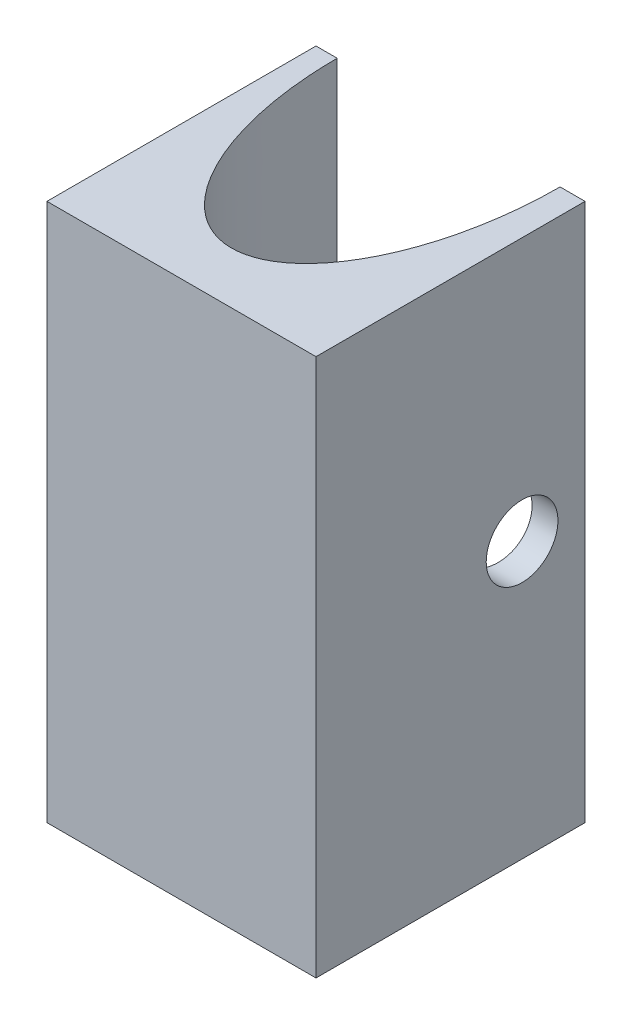
SolidWorks part; units mm, degrees
ref_plane "Front Plane" through (0, 0, 0) normal (0, 0, 1) x (1, 0, 0)
ref_plane "Top Plane" through (0, 0, 0) normal (0, 1, 0) x (1, 0, 0)
ref_plane "Right Plane" through (0, 0, 0) normal (1, 0, 0) x (0, 0, -1)
sketch "Sketch1" plane through (0, 0, 0) normal (0, 1, 0) x (1, 0, 0)
  line L1 (-48.6482, -19.1282) -> (-33.6482, -19.1282)
  line L2 (-48.6482, -19.1282) -> (-48.6482, -34.1282)
  line L3 (-48.6482, -34.1282) -> (-33.6482, -34.1282)
  line L4 (-33.6482, -19.1282) -> (-33.6482, -34.1282)
extrude "Boss-Extrude1" add sketch "Sketch1" along normal blind 30
sketch "Sketch2" plane through (0, 0, 0) normal (0, -1, 0) x (-1, 0, 0)
  line L1 (33.6482, -19.1282) -> (48.6482, -19.1282) construction
  ellipse E0 centre (41.2528, -19.1282) end of major axis (41.2528, -31.2407) minor radius 6.2128
extrude "Cut-Extrude3" cut sketch "Sketch2" against normal blind 30
sketch "Sketch3" plane through (-48.6482, 0, 0) normal (-1, 0, 0) x (0, 0, 1)
  circle A0 centre (22.639, 15.346) radius 2
extrude "Cut-Extrude4" cut sketch "Sketch3" against normal blind 30 contours A0
